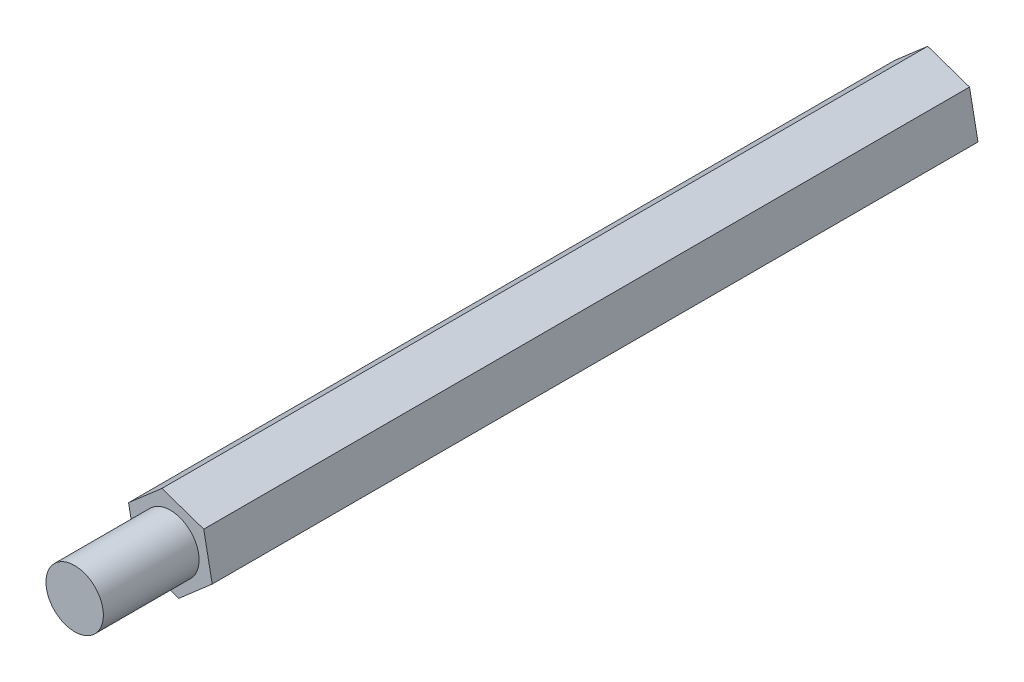
SolidWorks part; units mm, degrees
ref_plane "Front Plane" through (0, 0, 0) normal (0, 0, 1) x (1, 0, 0)
ref_plane "Top Plane" through (0, 0, 0) normal (0, 1, 0) x (1, 0, 0)
ref_plane "Right Plane" through (0, 0, 0) normal (1, 0, 0) x (0, 0, -1)
sketch "Sketch1" plane through (0, 0, 0) normal (0, 0, 1) x (1, 0, 0)
  line L1 (2.184, -0.7505) -> (1.742, 1.5162)
  line L2 (1.742, 1.5162) -> (-0.4421, 2.2667)
  line L3 (-0.4421, 2.2667) -> (-2.184, 0.7505)
  line L4 (-2.184, 0.7505) -> (-1.742, -1.5162)
  line L5 (-1.742, -1.5162) -> (0.4421, -2.2667)
  line L6 (0.4421, -2.2667) -> (2.184, -0.7505)
  circle A0 centre (0, 0) radius 2 construction
  dimension "D1" = 4
extrude "Boss-Extrude1" add sketch "Sketch1" along normal blind 40
sketch "Sketch2" plane through (0, 0, 40) normal (0, 0, 1) x (1, 0, 0)
  circle A0 centre (0, 0) radius 1.5
  dimension "D1" = 3
extrude "Boss-Extrude2" add sketch "Sketch2" along normal blind 5
